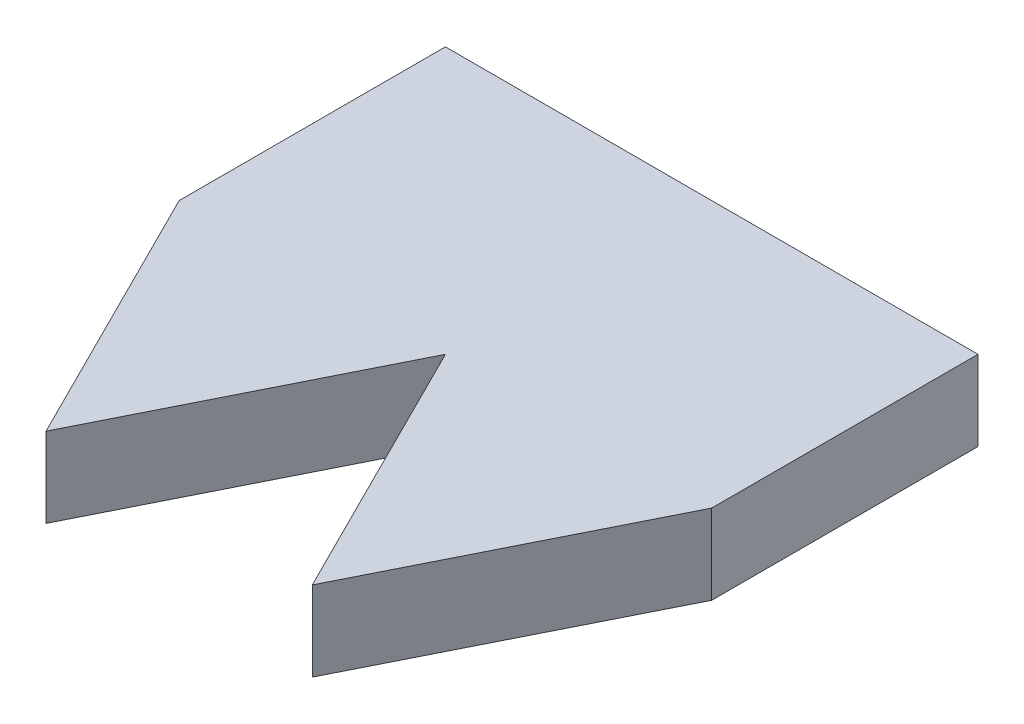
SolidWorks part; units mm, degrees
ref_plane "Front Plane" through (0, 0, 0) normal (0, 0, 1) x (1, 0, 0)
ref_plane "Top Plane" through (0, 0, 0) normal (0, 1, 0) x (1, 0, 0)
ref_plane "Right Plane" through (0, 0, 0) normal (1, 0, 0) x (0, 0, -1)
sketch "Sketch1" plane through (0, 0, 0) normal (0, 1, 0) x (1, 0, 0)
  line L1 (-10, -10) -> (10, -10)
  line L2 (-10, -10) -> (-10, 10)
  line L3 (-10, 10) -> (10, 10)
  line L4 (10, -10) -> (10, 10)
  line L5 (-10, -10) -> (10, 10) construction
  line L6 (-10, 10) -> (10, -10) construction
  point P0 (0, 0)
  dimension "D1" = 20
  dimension "D2" = 20
extrude "Boss-Extrude1" add sketch "Sketch1" along normal blind 3
sketch "Sketch2" plane through (0, 3, 0) normal (0, 1, 0) x (1, 0, 0)
  line L0 (-10, 0) -> (-5, -10)
  line L1 (-10, 10) -> (-10, -10) construction
  line L2 (-10, -10) -> (10, -10) construction
  line L3 (-5, -10) -> (0, 0)
  line L4 (0, 0) -> (5, -10)
  line L5 (5, -10) -> (10, 0)
  line L6 (10, -10) -> (10, 10) construction
  line L7 (10, 0) -> (10, -10)
  line L8 (10, -10) -> (-10, -10)
  line L9 (-10, -10) -> (-10, 0)
  point P6 (0, 0)
  line M1 (10, -10) -> (10, 10)
  line M3 (-10, 10) -> (-10, -10)
  line M4 (-10, -10) -> (10, -10)
  dimension "D1" = 5
  dimension "D2" = 5
extrude "Cut-Extrude1" cut sketch "Sketch2" against normal through all both and the other way through all contours L0 M3 M4 | L4 L3 M4 | L5 M4 M1
